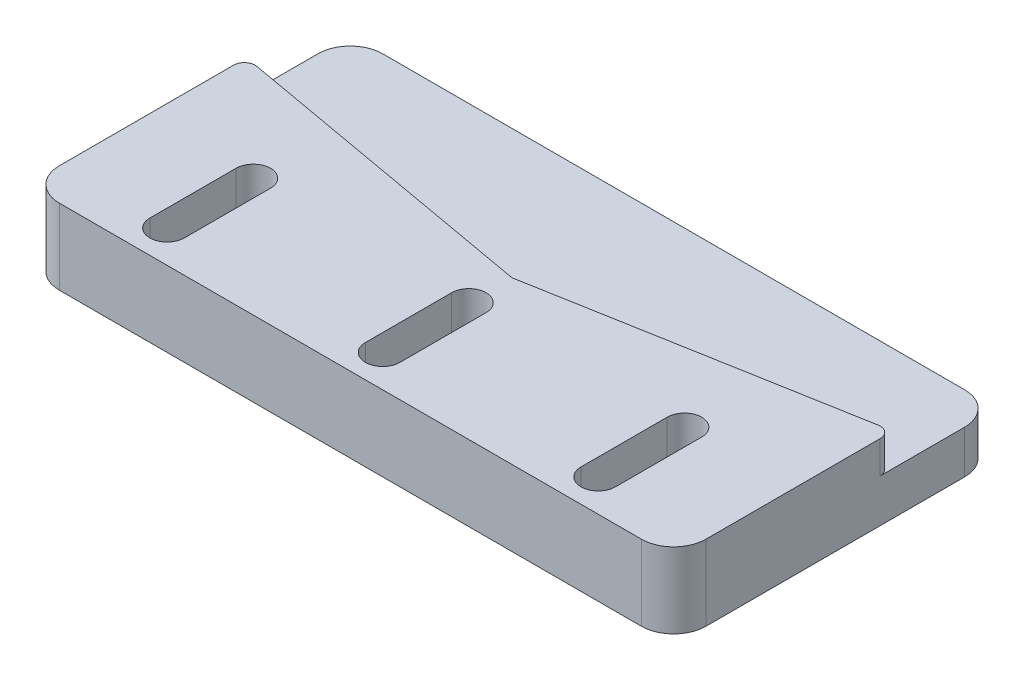
SolidWorks part; units mm, degrees
ref_plane "Front Plane" through (0, 0, 0) normal (0, 0, 1) x (1, 0, 0)
ref_plane "Top Plane" through (0, 0, 0) normal (0, 1, 0) x (1, 0, 0)
ref_plane "Right Plane" through (0, 0, 0) normal (1, 0, 0) x (0, 0, -1)
sketch "Sketch1" plane through (0, 0, 0) normal (0, 1, 0) x (1, 0, 0)
  line L1 (-30, -7.5) -> (30, -7.5)
  line L2 (-30, -7.5) -> (-30, 7.5)
  line L3 (-30, 7.5) -> (30, 7.5)
  line L4 (30, -7.5) -> (30, 7.5)
  line L5 (-30, -7.5) -> (30, 7.5) construction
  line L6 (-30, 7.5) -> (30, -7.5) construction
  point P0 (0, 0)
  dimension "D1" = 15
  dimension "D2" = 60
sketch "Sketch2" plane through (0, 0, 0) normal (0, 1, 0) x (1, 0, 0)
  line L0 (-30, 7.5) -> (30, 7.5) construction
  line L1 (-30, -7.5) -> (30, -7.5)
  line L2 (-30, -7.5) -> (-30, 11.6647)
  line L4 (30, -7.5) -> (30, 11.6647)
  arc A0 (-28.6548, 12.6032) -> (28.6548, 12.6032) centre (0, 90.5) ccw
  arc A1 (28.6548, 12.6032) -> (30, 11.6647) centre (29, 11.6647) cw
  arc A2 (-28.6548, 12.6032) -> (-30, 11.6647) centre (-29, 11.6647) ccw
  dimension "D1" = 83
  dimension "D2" = 1
extrude "Boss-Extrude1" add sketch "Sketch2" along normal blind 3
sketch "Sketch4" plane through (0, 0, 0) normal (0, -1, 0) x (1, 0, 0)
  line L1 (-30, 7.5) -> (30, 7.5)
  line L2 (-30, 7.5) -> (-30, -22.5)
  line L3 (-30, -22.5) -> (30, -22.5)
  line L4 (30, 7.5) -> (30, -22.5)
  dimension "D1" = 30
extrude "Boss-Extrude2" add sketch "Sketch4" along normal blind 4
fillet "Fillet1" radius 3 4 edges at (30, -2, -22.5) (30, -0.5, 7.5) (-30, -0.5, 7.5) (-30, -2, -22.5)
sketch "Sketch5" plane through (0, 3, 0) normal (0, 1, 0) x (1, 0, 0)
  line L0 (0, 3.5) -> (0, -4.5) construction
  line L1 (0, -54.6431) -> (0, 54.6431) construction
  line L2 (1.6, 3.5) -> (1.6, -4.5)
  line L3 (-1.6, 3.5) -> (-1.6, -4.5)
  line L4 (-30, -7.5) -> (30, -7.5) construction
  line L5 (20, 3.5) -> (20, -4.5) construction
  line L6 (21.6, 3.5) -> (21.6, -4.5)
  line L7 (18.4, 3.5) -> (18.4, -4.5)
  line L8 (0, 24.3668) -> (0, -20.2781) construction
  line L9 (-20, 3.5) -> (-20, -4.5) construction
  line L10 (-21.6, 3.5) -> (-21.6, -4.5)
  line L11 (-18.4, 3.5) -> (-18.4, -4.5)
  arc A0 (1.6, 3.5) -> (-1.6, 3.5) centre (0, 3.5) ccw
  arc A1 (-1.6, -4.5) -> (1.6, -4.5) centre (0, -4.5) ccw
  arc A2 (21.6, 3.5) -> (18.4, 3.5) centre (20, 3.5) ccw
  arc A3 (18.4, -4.5) -> (21.6, -4.5) centre (20, -4.5) ccw
  arc A4 (-21.6, 3.5) -> (-18.4, 3.5) centre (-20, 3.5) cw
  arc A5 (-18.4, -4.5) -> (-21.6, -4.5) centre (-20, -4.5) cw
  point P5 (0, -0.5)
  point P16 (20, -0.5)
  point P23 (-20, -0.5)
  dimension "D1" = 3.2
  dimension "D2" = 3
  dimension "D3" = 8
  dimension "D4" = 2
extrude "Cut-Extrude1" cut sketch "Sketch5" against normal through all
sketch "Sketch6" plane through (0, 3, 0) normal (0, 1, 0) x (1, 0, 0)
  line L0 (0, 7.5) -> (-28.8241, 12.6491)
  line L1 (-30, 7.5) -> (30, 7.5) construction
  line L5 (-27, -7.5) -> (27, -7.5)
  line L6 (30, -4.5) -> (30, 11.6647)
  line L7 (-30, 11.6647) -> (-30, -4.5)
  line L8 (-27, -7.5) -> (27, -7.5)
  line L9 (30, -4.5) -> (30, 11.6647)
  line L10 (-30, 11.6647) -> (-30, -4.5)
  line L11 (-18.4, -4.5) -> (-18.4, 3.5)
  line L12 (-21.6, 3.5) -> (-21.6, -4.5)
  line L13 (-18.4, -4.5) -> (-18.4, 3.5)
  line L14 (-21.6, 3.5) -> (-21.6, -4.5)
  line L15 (0, 7.5) -> (28.8241, 12.6491)
  line L16 (1.6, -4.5) -> (1.6, 3.5)
  line L17 (-1.6, 3.5) -> (-1.6, -4.5)
  line L18 (1.6, -4.5) -> (1.6, 3.5)
  line L19 (-1.6, 3.5) -> (-1.6, -4.5)
  line L21 (21.6, -4.5) -> (21.6, 3.5)
  line L22 (18.4, 3.5) -> (18.4, -4.5)
  line L23 (21.6, -4.5) -> (21.6, 3.5)
  line L24 (18.4, 3.5) -> (18.4, -4.5)
  arc A0 (-28.6548, 12.6032) -> (-30, 11.6647) centre (-29, 11.6647) ccw construction
  arc A1 (-28.6548, 12.6032) -> (-30, 11.6647) centre (-29, 11.6647) ccw construction
  arc A4 (-18.4, 3.5) -> (-21.6, 3.5) centre (-20, 3.5) ccw
  arc A5 (-21.6, -4.5) -> (-18.4, -4.5) centre (-20, -4.5) ccw
  arc A6 (-18.4, 3.5) -> (-21.6, 3.5) centre (-20, 3.5) ccw
  arc A7 (27, -7.5) -> (30, -4.5) centre (27, -4.5) ccw
  arc A8 (30, 11.6647) -> (28.6548, 12.6032) centre (29, 11.6647) ccw
  arc A9 (-28.6548, 12.6032) -> (28.6548, 12.6032) centre (0, 90.5) ccw
  arc A10 (-28.6548, 12.6032) -> (-30, 11.6647) centre (-29, 11.6647) ccw
  arc A11 (-30, -4.5) -> (-27, -7.5) centre (-27, -4.5) ccw
  arc A12 (27, -7.5) -> (30, -4.5) centre (27, -4.5) ccw
  arc A13 (30, 11.6647) -> (28.8241, 12.6491) centre (29, 11.6647) ccw
  arc A15 (-28.8241, 12.6491) -> (-30, 11.6647) centre (-29, 11.6647) ccw
  arc A16 (-30, -4.5) -> (-27, -7.5) centre (-27, -4.5) ccw
  arc A17 (-21.6, -4.5) -> (-18.4, -4.5) centre (-20, -4.5) ccw
  arc A18 (1.6, 3.5) -> (-1.6, 3.5) centre (0, 3.5) ccw
  arc A19 (-1.6, -4.5) -> (1.6, -4.5) centre (0, -4.5) ccw
  arc A20 (1.6, 3.5) -> (-1.6, 3.5) centre (0, 3.5) ccw
  arc A21 (-1.6, -4.5) -> (1.6, -4.5) centre (0, -4.5) ccw
  arc A22 (21.6, 3.5) -> (18.4, 3.5) centre (20, 3.5) ccw
  arc A23 (18.4, -4.5) -> (21.6, -4.5) centre (20, -4.5) ccw
  arc A24 (21.6, 3.5) -> (18.4, 3.5) centre (20, 3.5) ccw
  arc A25 (18.4, -4.5) -> (21.6, -4.5) centre (20, -4.5) ccw
  dimension "D1" = 0
  dimension "D2" = 0
  dimension "D3" = 0
  dimension "D4" = 0
extrude "Boss-Extrude3" add sketch "Sketch6" against normal up to surface (3 mm away) up to face at (0.1682, 0, -16.0844)
